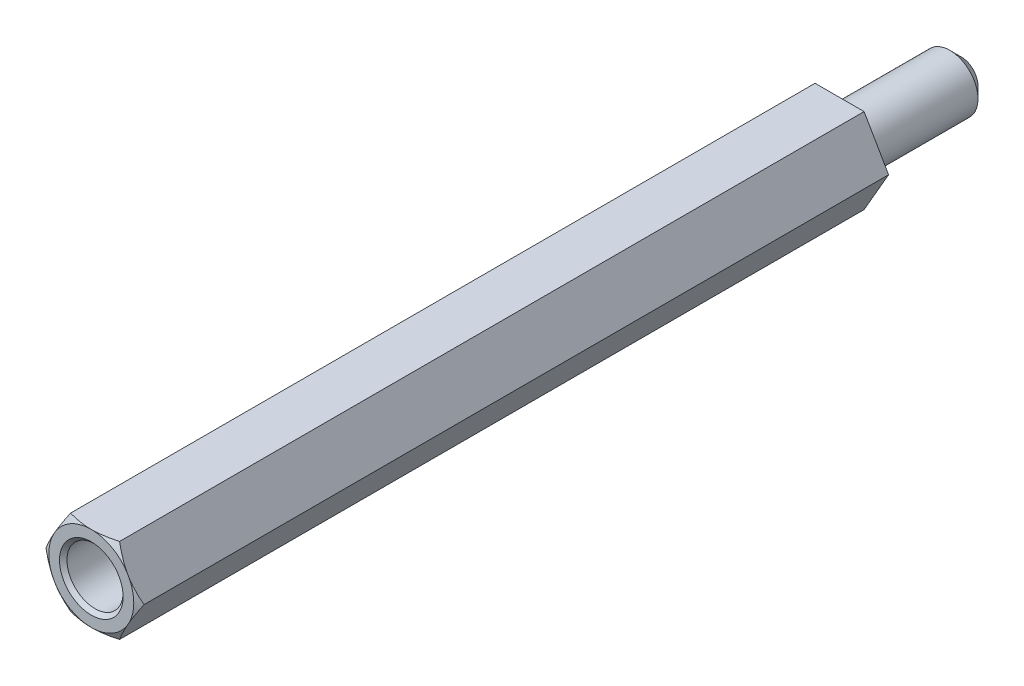
SolidWorks part; units mm, degrees
ref_plane "Front Plane" through (0, 0, 0) normal (0, 0, 1) x (1, 0, 0)
ref_plane "Top Plane" through (0, 0, 0) normal (0, 1, 0) x (1, 0, 0)
ref_plane "Right Plane" through (0, 0, 0) normal (1, 0, 0) x (0, 0, -1)
sketch "Sketch1" plane through (0, 0, 0) normal (0, 0, 1) x (1, 0, 0)
  line L0 (0, 0) -> (2.6212, 0) construction
  line L1 (2.6212, 0) -> (1.3106, 2.27)
  line L2 (1.3106, 2.27) -> (-1.3106, 2.27)
  line L3 (-1.3106, 2.27) -> (-2.6212, 0)
  line L4 (-2.6212, 0) -> (-1.3106, -2.27)
  line L5 (-1.3106, -2.27) -> (1.3106, -2.27)
  line L6 (1.3106, -2.27) -> (2.6212, 0)
  circle A0 centre (0, 0) radius 2.27 construction
  dimension "D1" = 4.54
extrude "Boss-Extrude1" add sketch "Sketch1" along normal blind 40
sketch "Sketch2" plane through (0, 0, 40) normal (0, 0, 1) x (1, 0, 0)
  circle A0 centre (0, 0) radius 1.5
extrude "Cut-Extrude1" cut sketch "Sketch2" against normal blind 12 and the other way through all
sketch "Sketch3" plane through (0, 0, 0) normal (0, 1, 0) x (1, 0, 0)
  line L0 (-2.6212, -40) -> (-2.2712, -40)
  line L1 (-2.2712, -40) -> (-2.6212, -39.8)
  line L2 (-2.6212, -40) -> (-2.6212, 0) construction
  line L3 (-2.6212, -39.8) -> (-2.6212, -40)
  dimension "D1" = 0.35
  dimension "D2" = 0.2
ref_axis "Axis1" through (0, 0, 28) along (0, 0, 1)
revolve "Cut-Revolve1" cut sketch "Sketch3" angle 360 about axis through (0, 0, 28) along (0, 0, 1)
ref_plane "Plane1" through (0, 0, 20) normal (0, 0, 1) x (1, 0, 0)
chamfer "Chamfer1" distance 0.2 angle 45 1 edges at (1.5, 0, 40)
sketch "Sketch4" plane through (0, 0, 0) normal (0, 0, -1) x (-1, 0, 0)
  circle A0 centre (0, 0) radius 1.5
extrude "Boss-Extrude2" add sketch "Sketch4" along normal blind 6.5
chamfer "Chamfer2" distance 0.6 angle 45 1 edges at (-1.5, 0, -6.5)
